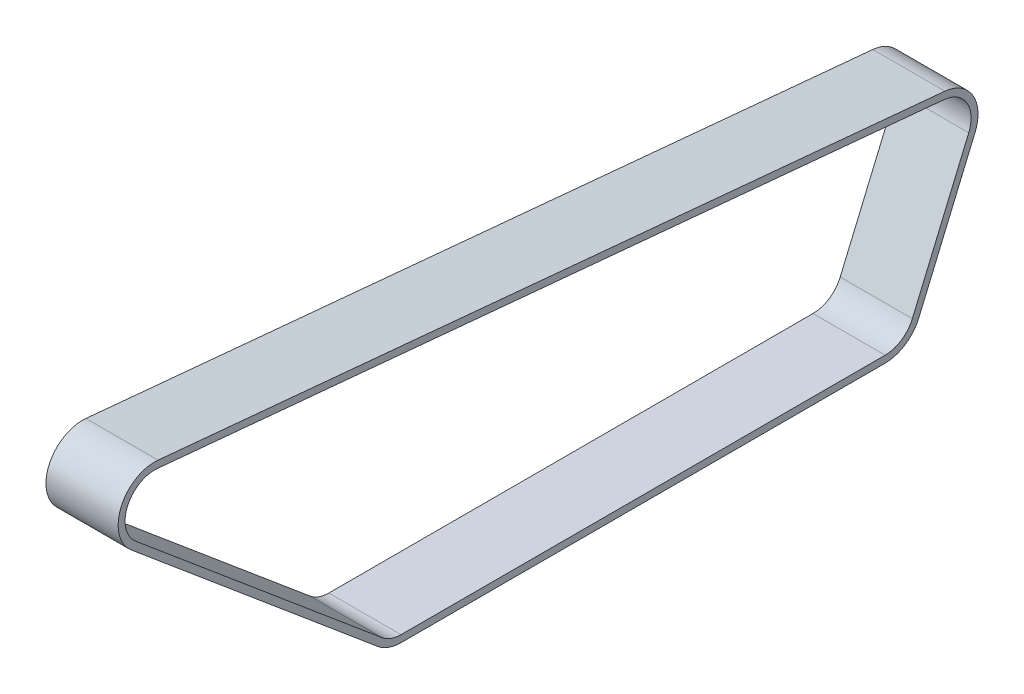
SolidWorks part; units mm, degrees
ref_plane "前视基准面" through (0, 0, 0) normal (0, 0, 1) x (1, 0, 0)
ref_plane "上视基准面" through (0, 0, 0) normal (0, 1, 0) x (1, 0, 0)
ref_plane "右视基准面" through (0, 0, 0) normal (1, 0, 0) x (0, 0, -1)
sketch "草图1" plane through (0, 0, 0) normal (1, 0, 0) x (0, 0, -1)
  line L0 (-132.3566, 0) -> (146.1004, 0)
  line L1 (-145.8552, 4.9131) -> (-287.5758, 123.8308)
  line L2 (-272.1132, 160.8256) -> (180.4951, 118.3099)
  line L4 (165.431, 12.7946) -> (197.8617, 89.1965)
  arc A0 (-132.3566, 0) -> (-145.8552, 4.9131) centre (-132.3566, 21) cw
  arc A1 (146.1004, 0) -> (165.431, 12.7946) centre (146.1004, 21) ccw
  arc A2 (197.8617, 89.1965) -> (180.4951, 118.3099) centre (178.5311, 97.4019) ccw
  arc A3 (-287.5758, 123.8308) -> (-272.1132, 160.8256) centre (-274.0772, 139.9177) cw
  point P3 (-140, 0)
  point P7 (160, 0)
  point P8 (160, 0)
  point P11 (209.0798, 115.6248)
  point P16 (-339.1716, 167.1248)
  point P33 (-140, 0)
  dimension "D4" = 260
  dimension "D8" = 113
  dimension "D10" = 278.457
  dimension "D5" = 21
  dimension "D6" = 83
  dimension "D1" = 300
  dimension "D2" = 140
  dimension "D3" = 140
extrude "凸台-拉伸1" add sketch "草图1" along normal blind 3
sketch "草图2" plane through (3, 0, 0) normal (1, 0, 0) x (0, 0, -1)
  line L0 (-272.1132, 160.8256) -> (180.4951, 118.3099)
  line L1 (197.8617, 89.1965) -> (165.431, 12.7946)
  line L2 (146.1004, 0) -> (-132.3566, 0)
  line L3 (-145.8552, 4.9131) -> (-287.5758, 123.8308)
  line L4 (-272.4873, 156.8432) -> (180.121, 114.3274)
  line L5 (194.1797, 90.7595) -> (161.749, 14.3576)
  line L6 (146.1004, 4) -> (-132.3566, 4)
  line L7 (-143.284, 7.9772) -> (-285.0046, 126.8949)
  arc A0 (180.4951, 118.3099) -> (197.8617, 89.1965) centre (178.5311, 97.4019) cw
  arc A1 (165.431, 12.7946) -> (146.1004, 0) centre (146.1004, 21) cw
  arc A2 (-145.8552, 4.9131) -> (-132.3566, 0) centre (-132.3566, 21) ccw
  arc A3 (-287.5758, 123.8308) -> (-272.1132, 160.8256) centre (-274.0772, 139.9177) cw
  arc A4 (180.121, 114.3274) -> (194.1797, 90.7595) centre (178.5311, 97.4019) cw
  arc A5 (161.749, 14.3576) -> (146.1004, 4) centre (146.1004, 21) cw
  arc A6 (-143.284, 7.9772) -> (-132.3566, 4) centre (-132.3566, 21) ccw
  arc A7 (-285.0046, 126.8949) -> (-272.4873, 156.8432) centre (-274.0772, 139.9177) cw
  dimension "D1" = 4
extrude "凸台-拉伸2" add sketch "草图2" along normal blind 38.5
sketch "草图4" plane through (3, 0, 0) normal (1, 0, 0) x (0, 0, -1)
  line L0 (-272.4873, 156.8432) -> (180.121, 114.3274)
  line L1 (194.1797, 90.7595) -> (161.749, 14.3576)
  line L2 (146.1004, 4) -> (-132.3566, 4)
  line L3 (-143.284, 7.9772) -> (-285.0046, 126.8949)
  arc A0 (-285.0046, 126.8949) -> (-272.4873, 156.8432) centre (-274.0772, 139.9177) cw
  arc A1 (180.121, 114.3274) -> (194.1797, 90.7595) centre (178.5311, 97.4019) cw
  arc A2 (161.749, 14.3576) -> (146.1004, 4) centre (146.1004, 21) cw
  arc A3 (-143.284, 7.9772) -> (-132.3566, 4) centre (-132.3566, 21) ccw
extrude "切除-拉伸5" cut sketch "草图4" against normal blind 3
